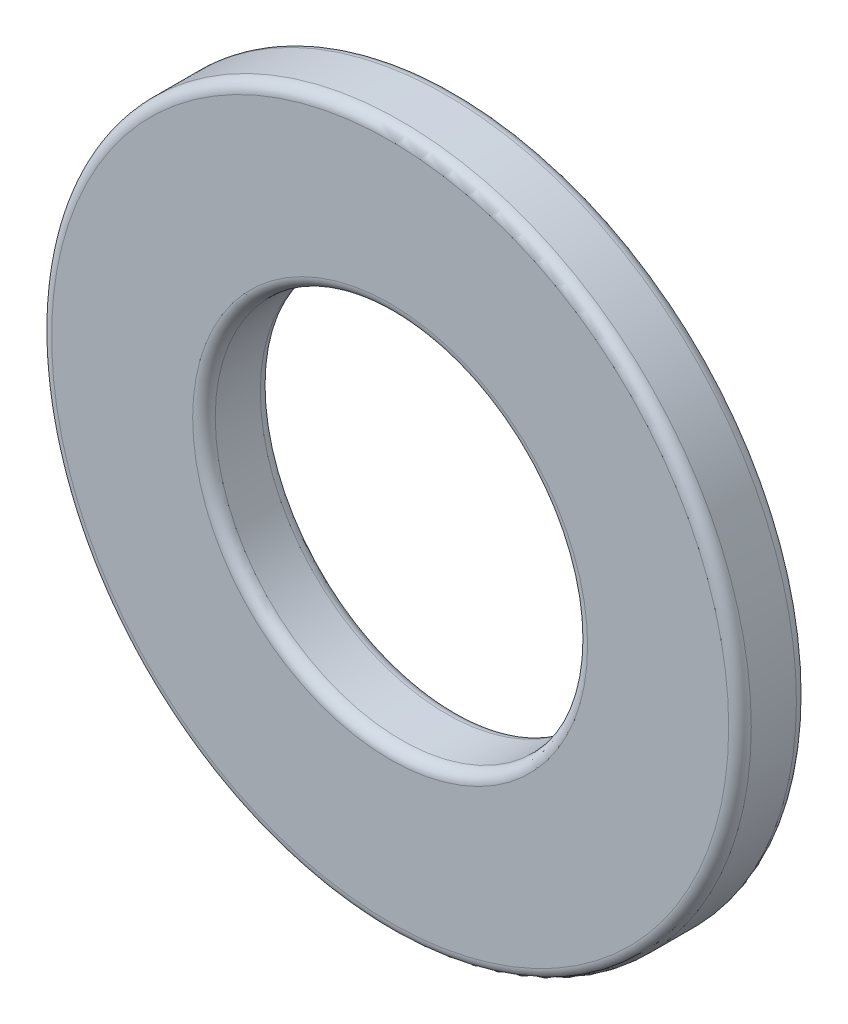
SolidWorks part; units mm, degrees
material "AISI Type 316L stainless steel"
ref_plane "Front Plane" through (0, 0, 0) normal (0, 0, 1) x (1, 0, 0)
ref_plane "Top Plane" through (0, 0, 0) normal (0, 1, 0) x (1, 0, 0)
ref_plane "Right Plane" through (0, 0, 0) normal (1, 0, 0) x (0, 0, -1)
sketch "Sketch1" plane through (0, 0, 0) normal (0, 0, 1) x (1, 0, 0)
  circle A0 centre (0, 0) radius 7.75
  circle A1 centre (0, 0) radius 4.125
  dimension "D1" = 15.5
  dimension "D2" = 8.25
extrude "Boss-Extrude1" add sketch "Sketch1" along normal blind 1.5
fillet "Fillet1" radius 0.25 4 edges at (4.125, 0, 0) (7.75, 0, 0) (4.125, 0, 1.5) (7.75, 0, 1.5)
